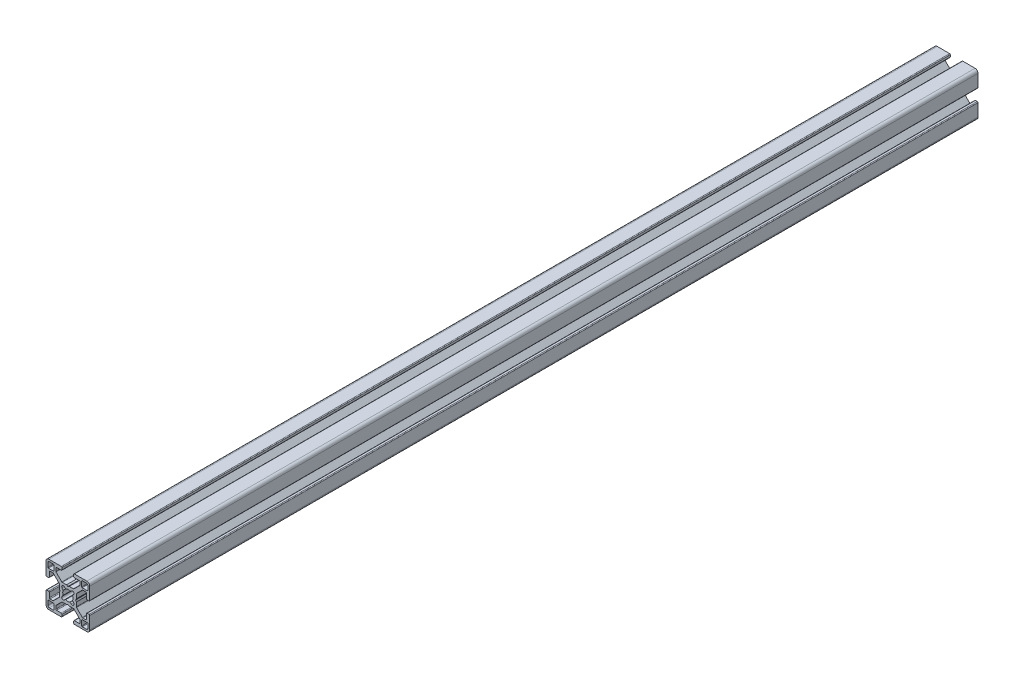
SolidWorks part; units mm, degrees
material "6105-T5 Aluminum"
ref_plane "Front Plane" through (0, 0, 0) normal (0, 0, 1) x (1, 0, 0)
ref_plane "Top Plane" through (0, 0, 0) normal (0, 1, 0) x (1, 0, 0)
ref_plane "Right Plane" through (0, 0, 0) normal (1, 0, 0) x (0, 0, -1)
sketch "Sketch1" plane through (0, 0, 0) normal (0, 0, 1) x (1, 0, 0)
  line L0 (9.5, -13.3189) -> (9.5, -9.88)
  line L1 (9.88, -9.5) -> (13.3189, -9.5)
  line L2 (13.6999, -9.881) -> (13.6999, -12.6999)
  line L3 (12.6999, -13.6999) -> (9.881, -13.6999)
  line L4 (-13.3189, -9.5) -> (-9.88, -9.5)
  line L5 (-9.5, -9.88) -> (-9.5, -13.3189)
  line L6 (-9.881, -13.6999) -> (-12.6999, -13.6999)
  line L7 (-13.6999, -12.6999) -> (-13.6999, -9.881)
  line L8 (-1.4942, -3.1981) -> (-2.4733, -3.9799)
  line L9 (-3.9799, -2.4733) -> (-3.1981, -1.4942)
  line L10 (-3.1981, 1.4942) -> (-3.9799, 2.4733)
  line L11 (-2.4733, 3.9799) -> (-1.4942, 3.1981)
  line L12 (1.4942, 3.1981) -> (2.4733, 3.9799)
  line L13 (3.9799, 2.4733) -> (3.1981, 1.4942)
  line L14 (3.1981, -1.4942) -> (3.9799, -2.4733)
  line L15 (2.4733, -3.9799) -> (1.4942, -3.1981)
  line L16 (-9.5, 13.3189) -> (-9.5, 9.88)
  line L17 (-9.88, 9.5) -> (-13.3189, 9.5)
  line L18 (-13.6999, 9.881) -> (-13.6999, 12.6999)
  line L19 (-12.6999, 13.6999) -> (-9.881, 13.6999)
  line L20 (9.881, 13.6999) -> (12.6999, 13.6999)
  line L21 (13.6999, 12.6999) -> (13.6999, 9.881)
  line L22 (13.3189, 9.5) -> (9.88, 9.5)
  line L23 (9.5, 9.88) -> (9.5, 13.3189)
  line L24 (12.7425, -4.5) -> (12.7425, -7.7325)
  line L25 (12.2428, -8.25) -> (10.2602, -8.25)
  line L26 (9.9066, -8.1035) -> (5.9811, -4.178)
  line L27 (5.8347, -3.8245) -> (5.8347, -1.0125)
  line L28 (5.8347, -1.0125) -> (5.3247, -0.0625)
  line L29 (5.3247, -0.0625) -> (5.8347, 0.8875)
  line L30 (5.8347, 0.8875) -> (5.8347, 3.8245)
  line L31 (5.9811, 4.178) -> (9.9066, 8.1035)
  line L32 (10.2602, 8.25) -> (12.2428, 8.25)
  line L33 (12.7425, 7.7325) -> (12.7425, 4.5)
  line L34 (13.2425, 4) -> (14.4999, 4)
  line L35 (14.9999, 4.5) -> (14.9999, 12.9999)
  line L36 (12.9999, 14.9999) -> (4.5, 14.9999)
  line L37 (4, 14.4999) -> (4, 13.2425)
  line L38 (4.5, 12.7425) -> (7.7325, 12.7425)
  line L39 (8.25, 12.2428) -> (8.25, 10.2602)
  line L40 (8.1035, 9.9066) -> (4.178, 5.9811)
  line L41 (3.8245, 5.8347) -> (0.95, 5.8347)
  line L42 (0.95, 5.8347) -> (0, 5.3247)
  line L43 (0, 5.3247) -> (-0.95, 5.8347)
  line L44 (-0.95, 5.8347) -> (-3.8245, 5.8347)
  line L45 (-4.178, 5.9811) -> (-8.1035, 9.9066)
  line L46 (-8.25, 10.2602) -> (-8.25, 12.2428)
  line L47 (-7.7325, 12.7425) -> (-4.5, 12.7425)
  line L48 (-4, 13.2425) -> (-4, 14.4999)
  line L49 (-4.5, 14.9999) -> (-12.9999, 14.9999)
  line L50 (-14.9999, 12.9999) -> (-14.9999, 4.5)
  line L51 (-14.4999, 4) -> (-13.2425, 4)
  line L52 (-12.7425, 4.5) -> (-12.7425, 7.7325)
  line L53 (-12.2428, 8.25) -> (-10.2602, 8.25)
  line L54 (-9.9066, 8.1035) -> (-5.9811, 4.178)
  line L55 (-5.8347, 3.8245) -> (-5.8347, 0.8875)
  line L56 (-5.8347, 0.8875) -> (-5.3247, -0.0625)
  line L57 (-5.3247, -0.0625) -> (-5.8347, -1.0125)
  line L58 (-5.8347, -1.0125) -> (-5.8347, -3.8245)
  line L59 (-5.9811, -4.178) -> (-9.9066, -8.1035)
  line L60 (-10.2602, -8.25) -> (-12.2428, -8.25)
  line L61 (-12.7425, -7.7325) -> (-12.7425, -4.5)
  line L62 (-13.2425, -4) -> (-14.4999, -4)
  line L63 (-14.9999, -4.5) -> (-14.9999, -12.9999)
  line L64 (-12.9999, -14.9999) -> (-4.5, -14.9999)
  line L65 (-4, -14.4999) -> (-4, -13.2425)
  line L66 (-4.5, -12.7425) -> (-7.7325, -12.7425)
  line L67 (-8.25, -12.2428) -> (-8.25, -10.2602)
  line L68 (-8.1035, -9.9066) -> (-4.178, -5.9811)
  line L69 (-3.8245, -5.8347) -> (-0.95, -5.8347)
  line L70 (-0.95, -5.8347) -> (0, -5.3247)
  line L71 (0, -5.3247) -> (0.95, -5.8347)
  line L72 (0.95, -5.8347) -> (3.8245, -5.8347)
  line L73 (4.178, -5.9811) -> (8.1035, -9.9066)
  line L74 (8.25, -10.2602) -> (8.25, -12.2428)
  line L75 (7.7325, -12.7425) -> (4.5, -12.7425)
  line L76 (4, -13.2425) -> (4, -14.4999)
  line L77 (4.5, -14.9999) -> (12.9999, -14.9999)
  line L78 (14.9999, -12.9999) -> (14.9999, -4.5)
  line L79 (14.4999, -4) -> (13.2425, -4)
  arc A0 (9.5, -13.3189) -> (9.881, -13.6999) centre (9.881, -13.3189) ccw
  arc A1 (9.88, -9.5) -> (9.5, -9.88) centre (9.88, -9.88) ccw
  arc A2 (13.6999, -9.881) -> (13.3189, -9.5) centre (13.3189, -9.881) ccw
  arc A3 (12.6999, -13.6999) -> (13.6999, -12.6999) centre (12.6999, -12.6999) ccw
  arc A4 (-13.3189, -9.5) -> (-13.6999, -9.881) centre (-13.3189, -9.881) ccw
  arc A5 (-9.5, -9.88) -> (-9.88, -9.5) centre (-9.88, -9.88) ccw
  arc A6 (-9.881, -13.6999) -> (-9.5, -13.3189) centre (-9.881, -13.3189) ccw
  arc A7 (-13.6999, -12.6999) -> (-12.6999, -13.6999) centre (-12.6999, -12.6999) ccw
  arc A8 (-1.4942, -3.1981) -> (1.4942, -3.1981) centre (0, 0) ccw
  arc A9 (-3.9799, -2.4733) -> (-2.4733, -3.9799) centre (-3.1422, -3.1422) ccw
  arc A10 (-3.1981, 1.4942) -> (-3.1981, -1.4942) centre (0, 0) ccw
  arc A11 (-2.4733, 3.9799) -> (-3.9799, 2.4733) centre (-3.1422, 3.1422) ccw
  arc A12 (1.4942, 3.1981) -> (-1.4942, 3.1981) centre (0, 0) ccw
  arc A13 (3.9799, 2.4733) -> (2.4733, 3.9799) centre (3.1422, 3.1422) ccw
  arc A14 (3.1981, -1.4942) -> (3.1981, 1.4942) centre (0, 0) ccw
  arc A15 (2.4733, -3.9799) -> (3.9799, -2.4733) centre (3.1422, -3.1422) ccw
  arc A16 (-9.5, 13.3189) -> (-9.881, 13.6999) centre (-9.881, 13.3189) ccw
  arc A17 (-9.88, 9.5) -> (-9.5, 9.88) centre (-9.88, 9.88) ccw
  arc A18 (-13.6999, 9.881) -> (-13.3189, 9.5) centre (-13.3189, 9.881) ccw
  arc A19 (-12.6999, 13.6999) -> (-13.6999, 12.6999) centre (-12.6999, 12.6999) ccw
  arc A20 (9.881, 13.6999) -> (9.5, 13.3189) centre (9.881, 13.3189) ccw
  arc A21 (13.6999, 12.6999) -> (12.6999, 13.6999) centre (12.6999, 12.6999) ccw
  arc A22 (13.3189, 9.5) -> (13.6999, 9.881) centre (13.3189, 9.881) ccw
  arc A23 (9.5, 9.88) -> (9.88, 9.5) centre (9.88, 9.88) ccw
  arc A24 (13.2425, -4) -> (12.7425, -4.5) centre (13.2425, -4.5) ccw
  arc A25 (12.2428, -8.25) -> (12.7425, -7.7325) centre (12.2428, -7.75) ccw
  arc A26 (9.9066, -8.1035) -> (10.2602, -8.25) centre (10.2602, -7.75) ccw
  arc A27 (5.8347, -3.8245) -> (5.9811, -4.178) centre (6.3347, -3.8245) ccw
  arc A28 (5.9811, 4.178) -> (5.8347, 3.8245) centre (6.3347, 3.8245) ccw
  arc A29 (10.2602, 8.25) -> (9.9066, 8.1035) centre (10.2602, 7.75) ccw
  arc A30 (12.7425, 7.7325) -> (12.2428, 8.25) centre (12.2428, 7.75) ccw
  arc A31 (12.7425, 4.5) -> (13.2425, 4) centre (13.2425, 4.5) ccw
  arc A32 (14.4999, 4) -> (14.9999, 4.5) centre (14.4999, 4.5) ccw
  arc A33 (14.9999, 12.9999) -> (12.9999, 14.9999) centre (12.9999, 12.9999) ccw
  arc A34 (4.5, 14.9999) -> (4, 14.4999) centre (4.5, 14.4999) ccw
  arc A35 (4, 13.2425) -> (4.5, 12.7425) centre (4.5, 13.2425) ccw
  arc A36 (8.25, 12.2428) -> (7.7325, 12.7425) centre (7.75, 12.2428) ccw
  arc A37 (8.1035, 9.9066) -> (8.25, 10.2602) centre (7.75, 10.2602) ccw
  arc A38 (3.8245, 5.8347) -> (4.178, 5.9811) centre (3.8245, 6.3347) ccw
  arc A39 (-4.178, 5.9811) -> (-3.8245, 5.8347) centre (-3.8245, 6.3347) ccw
  arc A40 (-8.25, 10.2602) -> (-8.1035, 9.9066) centre (-7.75, 10.2602) ccw
  arc A41 (-7.7325, 12.7425) -> (-8.25, 12.2428) centre (-7.75, 12.2428) ccw
  arc A42 (-4.5, 12.7425) -> (-4, 13.2425) centre (-4.5, 13.2425) ccw
  arc A43 (-4, 14.4999) -> (-4.5, 14.9999) centre (-4.5, 14.4999) ccw
  arc A44 (-12.9999, 14.9999) -> (-14.9999, 12.9999) centre (-12.9999, 12.9999) ccw
  arc A45 (-14.9999, 4.5) -> (-14.4999, 4) centre (-14.4999, 4.5) ccw
  arc A46 (-13.2425, 4) -> (-12.7425, 4.5) centre (-13.2425, 4.5) ccw
  arc A47 (-12.2428, 8.25) -> (-12.7425, 7.7325) centre (-12.2428, 7.75) ccw
  arc A48 (-9.9066, 8.1035) -> (-10.2602, 8.25) centre (-10.2602, 7.75) ccw
  arc A49 (-5.8347, 3.8245) -> (-5.9811, 4.178) centre (-6.3347, 3.8245) ccw
  arc A50 (-5.9811, -4.178) -> (-5.8347, -3.8245) centre (-6.3347, -3.8245) ccw
  arc A51 (-10.2602, -8.25) -> (-9.9066, -8.1035) centre (-10.2602, -7.75) ccw
  arc A52 (-12.7425, -7.7325) -> (-12.2428, -8.25) centre (-12.2428, -7.75) ccw
  arc A53 (-12.7425, -4.5) -> (-13.2425, -4) centre (-13.2425, -4.5) ccw
  arc A54 (-14.4999, -4) -> (-14.9999, -4.5) centre (-14.4999, -4.5) ccw
  arc A55 (-14.9999, -12.9999) -> (-12.9999, -14.9999) centre (-12.9999, -12.9999) ccw
  arc A56 (-4.5, -14.9999) -> (-4, -14.4999) centre (-4.5, -14.4999) ccw
  arc A57 (-4, -13.2425) -> (-4.5, -12.7425) centre (-4.5, -13.2425) ccw
  arc A58 (-8.25, -12.2428) -> (-7.7325, -12.7425) centre (-7.75, -12.2428) ccw
  arc A59 (-8.1035, -9.9066) -> (-8.25, -10.2602) centre (-7.75, -10.2602) ccw
  arc A60 (-3.8245, -5.8347) -> (-4.178, -5.9811) centre (-3.8245, -6.3347) ccw
  arc A61 (4.178, -5.9811) -> (3.8245, -5.8347) centre (3.8245, -6.3347) ccw
  arc A62 (8.25, -10.2602) -> (8.1035, -9.9066) centre (7.75, -10.2602) ccw
  arc A63 (7.7325, -12.7425) -> (8.25, -12.2428) centre (7.75, -12.2428) ccw
  arc A64 (4.5, -12.7425) -> (4, -13.2425) centre (4.5, -13.2425) ccw
  arc A65 (4, -14.4999) -> (4.5, -14.9999) centre (4.5, -14.4999) ccw
  arc A66 (12.9999, -14.9999) -> (14.9999, -12.9999) centre (12.9999, -12.9999) ccw
  arc A67 (14.9999, -4.5) -> (14.4999, -4) centre (14.4999, -4.5) ccw
extrude "Extrude1" add sketch "Sketch1" against normal blind 609.6
